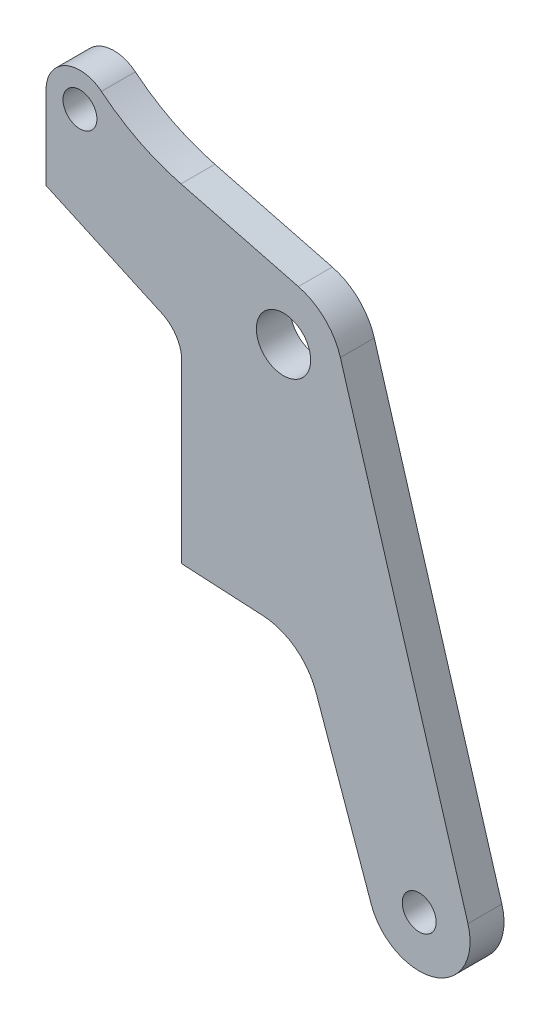
SolidWorks part; units mm, degrees
ref_plane "前视基准面" through (0, 0, 0) normal (0, 0, 1) x (1, 0, 0)
ref_plane "上视基准面" through (0, 0, 0) normal (0, 1, 0) x (1, 0, 0)
ref_plane "右视基准面" through (0, 0, 0) normal (1, 0, 0) x (0, 0, -1)
sketch "草图1" plane through (0, 0, 0) normal (0, 0, 1) x (1, 0, 0)
  line L0 (0.8743, 3.389) -> (-6.0435, 5.1738)
  line L1 (-14, 6) -> (-14, 1.11)
  line L2 (-6, -14.2004) -> (-1.2061, -14.4563)
  line L3 (1.9065, -16.7826) -> (5.1722, -26.0017)
  line L4 (10.8742, -24.1403) -> (3.3532, 1.003)
  line L5 (-12, 6) -> (8, -25) construction
  line L10 (-14, 1.11) -> (-7.17, -2.0053)
  line L12 (-6, -3.825) -> (-6, -14.2004)
  line L13 (0, 0) -> (8, -25) construction
  line L14 (0, 0) -> (-12, 6) construction
  arc A0 (-10.7348, 7.549) -> (-14, 6) centre (-12, 6) ccw
  arc A1 (5.1722, -26.0017) -> (10.8742, -24.1403) centre (8, -25) ccw
  arc A2 (0.8743, 3.389) -> (3.3532, 1.003) centre (0, 0) cw
  arc A3 (-6.0435, 5.1738) -> (-10.7348, 7.549) centre (-2.9818, 17.0414) cw
  arc A4 (-1.2061, -14.4563) -> (1.9065, -16.7826) centre (-1.3926, -17.9513) cw
  arc A5 (-7.17, -2.0053) -> (-6, -3.825) centre (-8, -3.825) cw
  circle A6 centre (-12, 6) radius 1
  circle A7 centre (8, -25) radius 1
  circle A8 centre (0, 0) radius 1.6
  dimension "D2" = 3
  dimension "D3" = 2
  dimension "D6" = 3.5
  dimension "D4" = 3.5
  dimension "D10" = 2
  dimension "D11" = 2
  dimension "D12" = 3.2
  dimension "D1" = 6
  dimension "D5" = 8
  dimension "D7" = 25
  dimension "D8" = 8
  dimension "D9" = 12
extrude "凸台-拉伸1" add sketch "草图1" against normal mid plane 2
hole_wizard "孔1" [suppressed] positions "草图8" profile "草图7" legacy
sketch "草图8" plane through (0, 0, 0) normal (0, 0, 1) x (1, 0, 0)
  point P0 (0, 0)
sketch "草图7" plane through (0, 0, 0) normal (1, 0, 0) x (0, -1, 0)
  line L0 (0, 0) -> (0, 2)
  line L1 (0, 2) -> (1.5, 2)
  line L2 (1.5, 2) -> (1.5, 1.5)
  line L3 (1.5, 1.5) -> (3, 0)
  line L4 (3, 0) -> (0, 0)
  line L5 (0, -6.4453) -> (0, 115.525) construction
  line L6 (-1.5, 1.5) -> (-3, 0) construction
  dimension "直径" = 3
  dimension "深度" = 2
  dimension "锥坑角度" = 90
  dimension "锥坑直径" = 6
